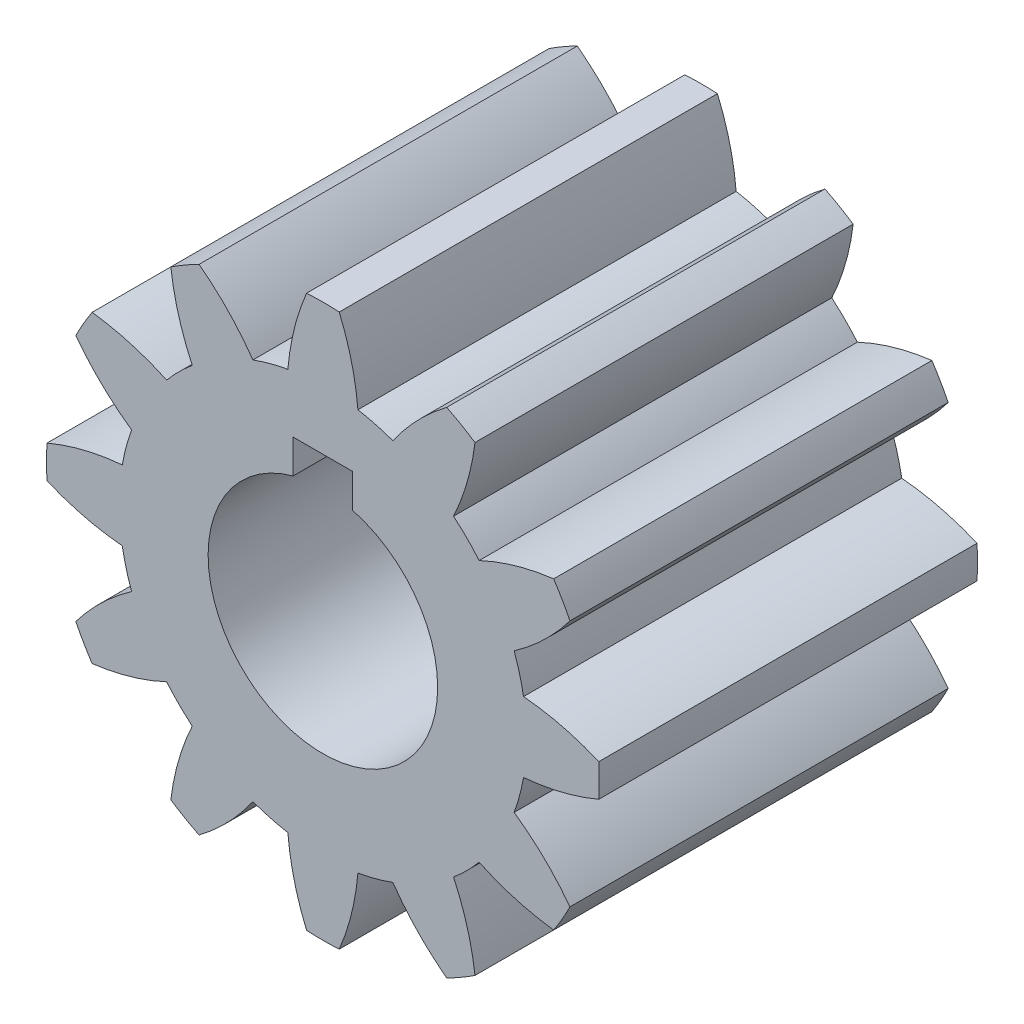
SolidWorks part; units mm, degrees
material "AISI 4130 Steel, normalized at 870C"
ref_plane "Front Plane" through (0, 0, 0) normal (0, 0, 1) x (1, 0, 0)
ref_plane "Top Plane" through (0, 0, 0) normal (0, 1, 0) x (1, 0, 0)
ref_plane "Right Plane" through (0, 0, 0) normal (1, 0, 0) x (0, 0, -1)
sketch "Sketch1" plane through (0, 0, 0) normal (0, 0, 1) x (1, 0, 0)
  circle A0 centre (0, 0) radius 7.112
  circle A1 centre (0, 0) radius 4.0081
  dimension "D1" = 8.0162
  dimension "D2" = 14.224
extrude "Extrude1" add sketch "Sketch1" along normal mid plane 13.208
sketch "Sketch2" plane through (0, 0, 0) normal (0, 0, 1) x (1, 0, 0)
  line L0 (0, 0) -> (0, 15.3026) construction
  line L1 (0, 0) -> (1.9689, 6.834) construction
  arc A0 (-1.2232, 7.006) -> (1.2232, 7.006) centre (0, 0) cw
  circle A1 centre (0, 0) radius 7.112 construction
  arc A4 (-0.5697, 9.6352) -> (-1.2232, 7.006) centre (7.3719, 6.2653) ccw
  arc A5 (0.5697, 9.6352) -> (-0.5697, 9.6352) centre (0, 0) ccw
  arc A6 (1.2232, 7.006) -> (0.5697, 9.6352) centre (-7.3719, 6.2653) ccw
  arc A7 (1.9689, 6.834) -> (1.2232, 7.006) centre (0, 0) ccw construction
  dimension "D1" = 9.652
  dimension "D2" = 8.627
  dimension "D3" = 16.071
  dimension "D4" = 1.1394
  dimension "D6" = 1.2232
extrude "Extrude2" add sketch "Sketch2" along normal through all and the other way through all
pattern_circular "CirPattern1" count 12 over 360 about axis through (0, 0, 0) along (0, 0, 1) of "Extrude2"
sketch "Sketch3" plane through (0, 0, 6.604) normal (0, 0, 1) x (1, 0, 0)
  line L0 (-1.0414, 3.8705) -> (-1.0414, 5.0483)
  line L1 (1.0414, 5.0483) -> (-1.0414, 5.0483)
  line L2 (1.0414, 5.0483) -> (1.0414, 3.8705)
  line L3 (0, 0) -> (0, 12.0198) construction
  circle A0 centre (0, 0) radius 4.0081 construction
  arc A1 (1.0414, 3.8705) -> (-1.0414, 3.8705) centre (0, 0) ccw
  circle M49 centre (0, 0) radius 4.0081
  dimension "D1" = 2.0828
  dimension "D2" = 5.0483
extrude "Extrude3" cut sketch "Sketch3" against normal through all contours L3 A1 L2 L1 | L3 L1 L0 M49
